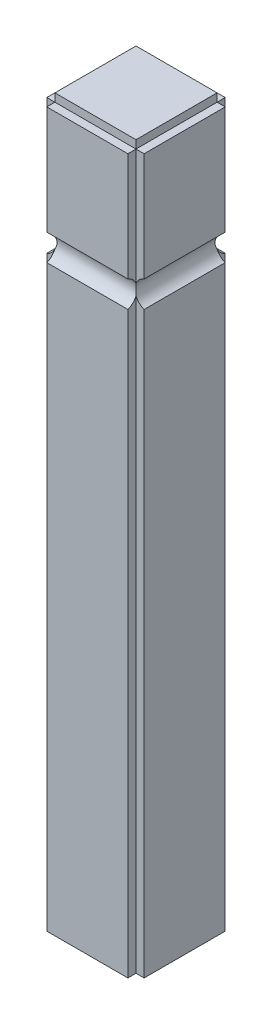
SolidWorks part; units mm, degrees
ref_plane "前视基准面" through (0, 0, 0) normal (0, 0, 1) x (1, 0, 0)
ref_plane "上视基准面" through (0, 0, 0) normal (0, 1, 0) x (1, 0, 0)
ref_plane "右视基准面" through (0, 0, 0) normal (1, 0, 0) x (0, 0, -1)
sketch "草图4" plane through (0, 0, 0) normal (0, 1, 0) x (1, 0, 0)
  line L1 (0, 0) -> (180, 0)
  line L2 (0, 0) -> (0, 180)
  line L3 (0, 180) -> (180, 180)
  line L4 (180, 0) -> (180, 180)
  dimension "D1" = 180
  dimension "D2" = 180
extrude "凸台-拉伸1" add sketch "草图4" against normal blind 1320
sketch "草图5" plane through (0, 0, 0) normal (0, 1, 0) x (1, 0, 0)
  line L1 (0, 180) -> (15, 180)
  line L2 (0, 180) -> (0, 165)
  line L3 (0, 165) -> (15, 165)
  line L4 (15, 180) -> (15, 165)
  line L5 (0, 0) -> (15, 0)
  line L6 (0, 0) -> (0, 15)
  line L7 (0, 15) -> (15, 15)
  line L8 (15, 0) -> (15, 15)
  line L9 (180, 180) -> (165, 180)
  line L10 (180, 180) -> (180, 165)
  line L11 (180, 165) -> (165, 165)
  line L12 (165, 180) -> (165, 165)
  line L13 (180, 0) -> (165, 0)
  line L14 (180, 0) -> (180, 15)
  line L15 (180, 15) -> (165, 15)
  line L16 (165, 0) -> (165, 15)
  dimension "D1" = 15
  dimension "D2" = 15
  dimension "D3" = 15
  dimension "D4" = 15
  dimension "D5" = 15
  dimension "D6" = 15
  dimension "D7" = 15
  dimension "D8" = 15
extrude "切除-拉伸1" cut sketch "草图5" against normal blind 1320
sketch "草图6" plane through (0, 0, 0) normal (0, 0, 1) x (1, 0, 0)
  line L0 (0, -1320) -> (0, 0) construction
  line L1 (180, -1320) -> (180, 0) construction
  line L2 (0, -200.6074) -> (0, -249.3926)
  line L3 (180, -200.6074) -> (180, -249.3926)
  arc A0 (0, -249.3926) -> (0, -200.6074) centre (-9, -225) ccw
  arc A1 (180, -200.6074) -> (180, -249.3926) centre (189, -225) ccw
  point P0 (-9, -225)
  point P1 (189, -225)
  dimension "D5" = 52
  dimension "D6" = 52
  dimension "D1" = 225
  dimension "D2" = 225
  dimension "D3" = 9
  dimension "D4" = 9
extrude "切除-拉伸2" cut sketch "草图6" against normal through all both and the other way through all
sketch "草图7" plane through (0, 0, 0) normal (-1, 0, 0) x (0, 0, 1)
  line L0 (-180, -215) -> (-180, -235) construction
  line L1 (0, -235) -> (0, -215) construction
  line L2 (-165, 0) -> (-15, 0) construction
  line L3 (-180, -200.6074) -> (-180, -249.3926)
  line L4 (-180, -215) -> (-180, 0) construction
  line L5 (-180, -1320) -> (-180, -235) construction
  line L6 (0, -200.6074) -> (0, -249.3926)
  line L7 (0, -1320) -> (0, -235) construction
  arc A0 (-180, -249.3926) -> (-180, -200.6074) centre (-189, -225) ccw
  arc A1 (0, -200.6074) -> (0, -249.3926) centre (9, -225) ccw
  point P0 (-189, -225)
  point P1 (9, -225)
  dimension "D1" = 9
  dimension "D5" = 52
  dimension "D6" = 52
  dimension "D2" = 9
  dimension "D3" = 225
  dimension "D4" = 225
extrude "切除-拉伸3" cut sketch "草图7" against normal through all
sketch "草图8" plane through (0, 0, 0) normal (0, 1, 0) x (1, 0, 0)
  line L0 (15, 15) -> (165, 15)
  line L1 (165, 15) -> (165, 165)
  line L2 (165, 165) -> (15, 165)
  line L3 (15, 165) -> (15, 15)
extrude "凸台-拉伸2" add sketch "草图8" along normal blind 15
